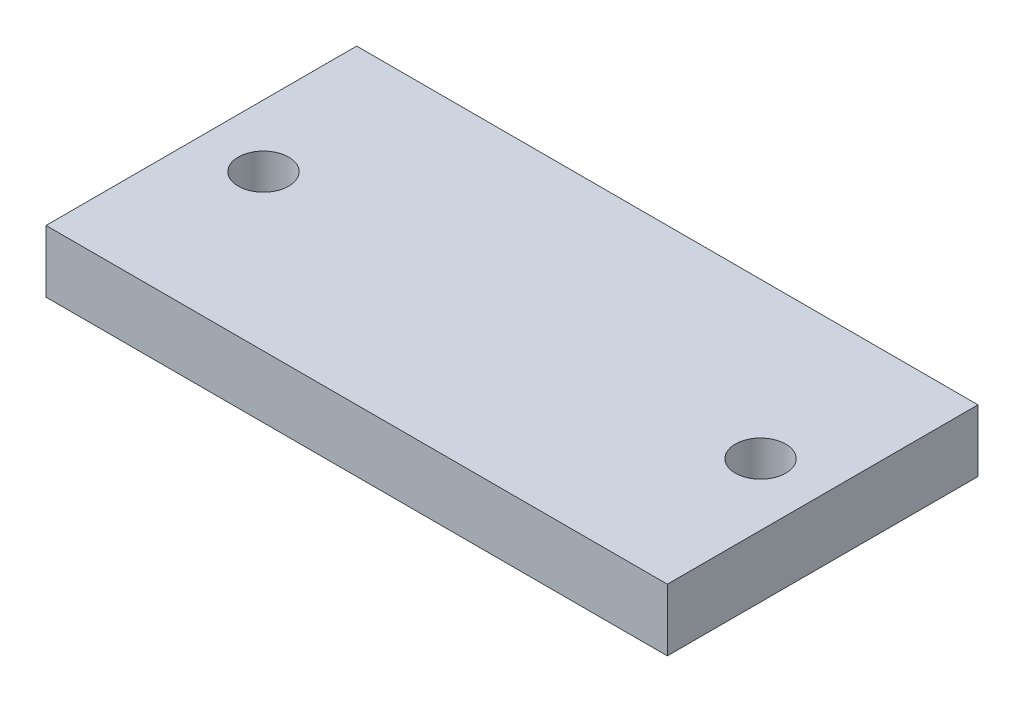
SolidWorks part; units mm, degrees
ref_plane "Front Plane" through (0, 0, 0) normal (0, 0, 1) x (1, 0, 0)
ref_plane "Top Plane" through (0, 0, 0) normal (0, 1, 0) x (1, 0, 0)
ref_plane "Right Plane" through (0, 0, 0) normal (1, 0, 0) x (0, 0, -1)
sketch "Sketch1" plane through (0, 0, 0) normal (0, 1, 0) x (1, 0, 0)
  line L0 (0, 63.5) -> (254, 63.5) construction
  line L1 (0, 0) -> (254, 0)
  line L2 (0, 0) -> (0, 127)
  line L3 (0, 127) -> (254, 127)
  line L4 (254, 0) -> (254, 127)
  line L5 (127, 85.725) -> (127, 15.875) construction
  line L10 (73.025, 63.5) -> (180.975, 63.5) construction
  line L11 (127, 127) -> (127, 0) construction
  circle A0 centre (25.4, 63.5) radius 10.3188
  circle A1 centre (228.6, 63.5) radius 10.3187
  dimension "D3" = 20.6375
  dimension "D4" = 25.4
  dimension "D5" = 25.4
  dimension "D1" = 127
  dimension "D2" = 254
extrude "Boss-Extrude1" add sketch "Sketch1" along normal blind 25.4
